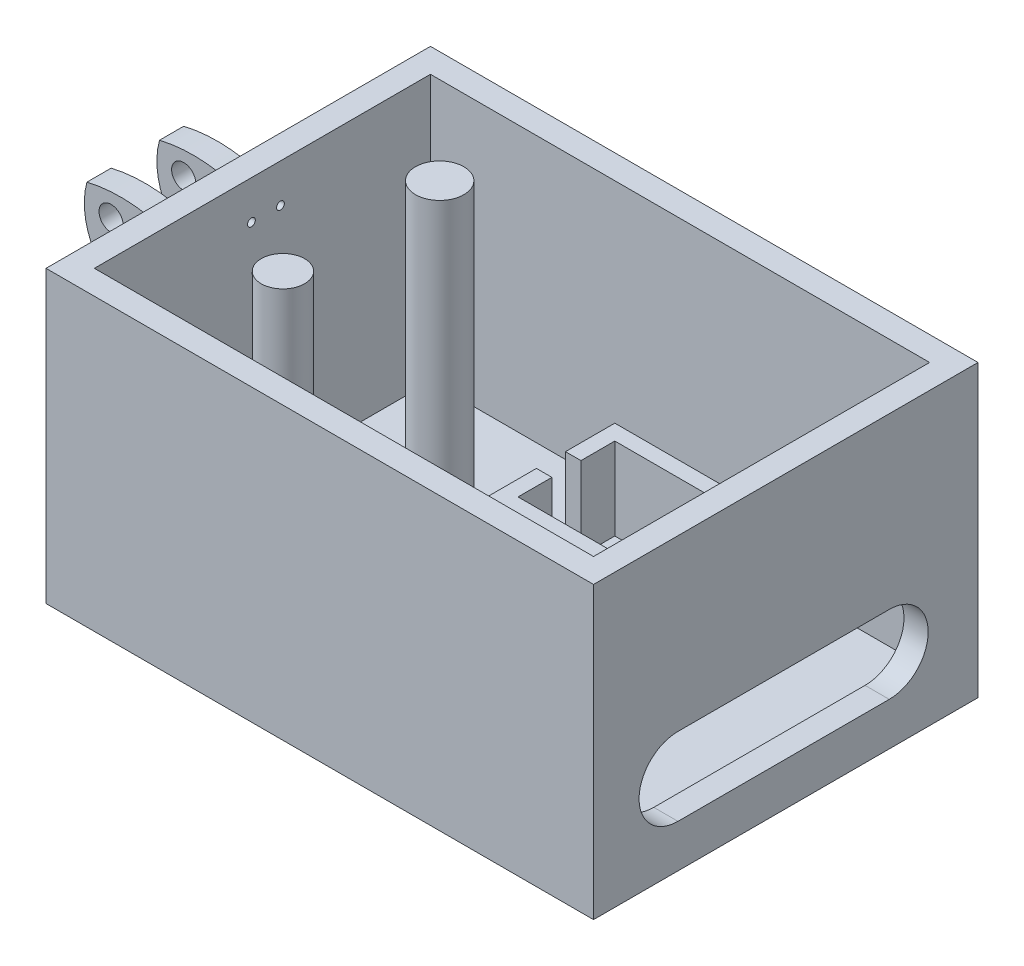
SolidWorks part; units mm, degrees
ref_plane "Front Plane" through (0, 0, 0) normal (0, 0, 1) x (1, 0, 0)
ref_plane "Top Plane" through (0, 0, 0) normal (0, 1, 0) x (1, 0, 0)
ref_plane "Right Plane" through (0, 0, 0) normal (1, 0, 0) x (0, 0, -1)
ref_plane "Palm Side Plane" through (0, 38.1, 0) normal (0, 1, 0) x (1, 0, 0)
ref_plane "Left Side Plane" through (0, 0, 63.5) normal (0, 0, 1) x (1, 0, 0)
ref_plane "Top Side Plane" through (-69.85, 0, 0) normal (1, 0, 0) x (0, 0, -1)
ref_plane "Wrist Plane" through (62.9138, 0, 0) normal (1, 0, 0) x (0, 0, -1)
sketch "Hand Direction Arrow" plane through (0, 38.1, 0) normal (0, 1, 0) x (1, 0, 0)
  line L0 (49.8191, -114.0829) -> (-36.738, -114.0829) construction
  line L1 (-36.738, -114.0829) -> (-22.4792, -131.555) construction
  line L2 (-36.738, -114.0829) -> (-22.4792, -99.8241) construction
sketch "Sketch2" plane through (0, 0, 0) normal (0, 1, 0) x (1, 0, 0)
  line L5 (-69.85, -63.5) -> (69.85, 63.5) construction
  line L6 (-69.85, 63.5) -> (69.85, -63.5) construction
  line L7 (-20.7784, 52.7587) -> (-36.189, 52.7587)
  line L8 (-36.189, 52.7587) -> (-36.189, 33.7087)
  line L16 (-38.8642, 27.3587) -> (-36.189, 33.7087)
  line L19 (15.3118, -63.2103) -> (-3.7382, -63.2103)
  line L20 (-3.7382, -63.2103) -> (-3.7382, -58.593)
  line L21 (22.9098, -62.5249) -> (22.9098, 48.896)
  line L22 (-48.9477, 8.3087) -> (-48.9477, 27.3587)
  line L23 (-48.9477, 27.3587) -> (-38.8642, 27.3587)
  line L24 (-48.9477, 8.3087) -> (-48.9477, -42.4913)
  line L25 (-42.9594, -42.4913) -> (-48.9477, -42.4913)
  arc A0 (22.9098, 48.896) -> (-20.7784, 52.7587) centre (-16.6219, -149.2259) ccw
  arc A2 (-42.9594, -42.4913) -> (-16.4221, -49.7553) centre (-56.8306, -145.2734) cw
  arc A5 (-3.7382, -58.593) -> (-16.4221, -49.7553) centre (16.7508, -15.6666) cw
  arc A6 (15.3118, -63.2103) -> (22.9098, -62.5249) centre (14.5642, -12.4678) ccw
  point P0 (0, 0)
  dimension "D1" = 19.05
  dimension "D4" = 19.05
  dimension "D5" = 19.05
  dimension "D6" = 6.35
extrude "Boss-Extrude1" add sketch "Sketch2" along normal blind 38.1
sketch "Sketch3" plane through (0, 38.1, 0) normal (0, 1, 0) x (1, 0, 0)
  line L5 (-45.7727, 24.1837) -> (19.7348, 24.1837)
  line L6 (22.9098, -62.5249) -> (22.9098, 48.896) construction
  line L24 (-45.7727, 7.713) -> (-45.7727, 24.1837)
  line L26 (-48.9477, 27.3587) -> (-48.9477, -42.4913) construction
  line L41 (-38.8642, 27.3587) -> (22.9098, 27.3587)
  line L42 (-45.7727, 7.713) -> (-45.7727, -19.9216)
  line L44 (-45.7727, -19.9216) -> (19.7348, -19.9216)
  line L45 (19.7348, -19.9216) -> (19.7348, 24.1837)
  line L46 (-48.9477, -23.0966) -> (22.9098, -23.0966)
  line L47 (-48.9477, -55.2233) -> (-48.9477, -23.0966)
  line L48 (-48.9477, 27.3587) -> (-48.9477, -42.4913) construction
  arc A7 (-48.9477, -55.2233) -> (22.9098, -23.0966) centre (8.6461, -87.618) ccw
  arc A11 (-38.8642, 27.3587) -> (22.9098, 27.3587) centre (-7.9772, 76.0331) cw
  point P0 (0, 0)
  point P6 (-45.5127, -25.7954)
  point P29 (-45.5127, -25.7954)
  dimension "D2" = 3.175
  dimension "D3" = 3.175
  dimension "D4" = 3.175
  dimension "D11" = 3.175
extrude "Cut-Extrude1" cut sketch "Sketch3" against normal blind 34.925
sketch "Sketch6" plane through (0, 0, 0) normal (0, 1, 0) x (1, 0, 0)
  line L0 (-18.154, -9.4667) -> (-16.122, -9.4667)
  line L7 (8.008, -13.9117) -> (-16.122, -13.9117)
  line L8 (8.008, -13.9117) -> (8.008, -9.4667)
  line L9 (8.008, -1.2117) -> (-16.122, -1.2117)
  line L10 (-16.122, -13.9117) -> (-16.122, -9.4667)
  line L11 (8.008, -13.9117) -> (-16.122, -1.2117) construction
  line L12 (8.008, -1.2117) -> (-16.122, -13.9117) construction
  line L13 (10.04, -15.9437) -> (-18.154, -15.9437)
  line L14 (10.04, -15.9437) -> (10.04, -9.4667)
  line L15 (10.04, 0.8203) -> (-18.154, 0.8203)
  line L16 (-18.154, -15.9437) -> (-18.154, -9.4667)
  line L17 (10.04, -15.9437) -> (-18.154, 0.8203) construction
  line L18 (10.04, 0.8203) -> (-18.154, -15.9437) construction
  line L19 (-18.154, -5.6567) -> (-16.122, -5.6567)
  line L20 (-18.154, -5.6567) -> (-18.154, 0.8203)
  line L21 (-16.122, -5.6567) -> (-16.122, -1.2117)
  line L22 (8.008, -9.4667) -> (10.04, -9.4667)
  line L23 (8.008, -5.6567) -> (10.04, -5.6567)
  line L24 (8.008, -5.6567) -> (8.008, -1.2117)
  line L25 (10.04, -5.6567) -> (10.04, 0.8203)
  point P0 (26.0547, 16.5381)
  point P6 (-4.057, -7.5617)
  point P29 (-4.057, -7.5617)
  dimension "D6" = 2.032
  dimension "D7" = 2.032
  dimension "D9" = 12.7
  dimension "D10" = 24.13
  dimension "D11" = 4.445
  dimension "D12" = 4.445
  dimension "D13" = 4.445
  dimension "D14" = 4.445
extrude "Servo Box 1" add sketch "Sketch6" along normal blind 13.97
sketch "Sketch7" plane through (0, 0, 0) normal (0, 1, 0) x (1, 0, 0)
  line L0 (-18.154, 10.4723) -> (-16.122, 10.4723)
  line L5 (10.04, 0.8203) -> (-18.154, 0.8203) construction
  line L6 (-18.154, 0.8203) -> (-18.154, -5.6567) construction
  line L7 (8.008, 6.0273) -> (-16.122, 6.0273)
  line L8 (8.008, 6.0273) -> (8.008, 10.4723)
  line L9 (8.008, 18.7273) -> (-16.122, 18.7273)
  line L10 (-16.122, 6.0273) -> (-16.122, 10.4723)
  line L11 (8.008, 6.0273) -> (-16.122, 18.7273) construction
  line L12 (8.008, 18.7273) -> (-16.122, 6.0273) construction
  line L13 (10.04, 3.9953) -> (-18.154, 3.9953)
  line L14 (10.04, 3.9953) -> (10.04, 10.4723)
  line L15 (10.04, 20.7593) -> (-18.154, 20.7593)
  line L16 (-18.154, 3.9953) -> (-18.154, 10.4723)
  line L17 (10.04, 3.9953) -> (-18.154, 20.7593) construction
  line L18 (10.04, 20.7593) -> (-18.154, 3.9953) construction
  line L19 (-18.154, 14.2823) -> (-16.122, 14.2823)
  line L20 (-18.154, 14.2823) -> (-18.154, 20.7593)
  line L21 (-16.122, 14.2823) -> (-16.122, 18.7273)
  line L22 (8.008, 10.4723) -> (10.04, 10.4723)
  line L23 (8.008, 14.2823) -> (10.04, 14.2823)
  line L24 (8.008, 14.2823) -> (8.008, 18.7273)
  line L25 (10.04, 14.2823) -> (10.04, 20.7593)
  point P0 (-14.8998, -5.4903)
  point P6 (-4.057, 12.3773)
  point P29 (-4.057, 12.3773)
  dimension "D2" = 3.175
  dimension "D3" = 0
  dimension "D6" = 2.032
  dimension "D7" = 2.032
  dimension "D9" = 12.7
  dimension "D10" = 24.13
  dimension "D11" = 4.445
  dimension "D12" = 4.445
  dimension "D13" = 4.445
  dimension "D14" = 4.445
extrude "Servo Box 2" add sketch "Sketch7" along normal blind 13.97
ref_plane "Pinky Attachment Plane" through (0, 0, -52.7587) normal (0, 0, -1) x (-1, 0, 0)
ref_plane "Ring Attachment Plane" through (0, 0, -12.1187) normal (0, 0, -1) x (-1, 0, 0)
ref_plane "Middle Attachment Plane" through (0, 0, 13.2813) normal (0, 0, -1) x (-1, 0, 0)
ref_plane "Pointer Attachment Plane" through (0, 0, 38.6813) normal (0, 0, -1) x (-1, 0, 0)
ref_plane "Thumb Attachment Plane" through (-3.7382, 0, 0) normal (-1, 0, 0) x (0, 0, 1)
sketch "Sketch36" plane through (0, 0, -12.1187) normal (0, 0, -1) x (-1, 0, 0)
  line L3 (48.9477, 29.21) -> (48.9477, 18.0742)
  line L5 (48.9477, 18.0742) -> (53.3927, 18.0742)
  line L6 (53.3927, 38.1) -> (53.3927, 18.0742) construction
  line L7 (48.9477, 38.1) -> (48.9477, 0) construction
  line L8 (53.3927, 18.0742) -> (59.7427, 18.0742)
  line L9 (59.7427, 18.0742) -> (59.7427, 21.2492)
  line L10 (-22.9098, 38.1) -> (48.9477, 38.1) construction
  arc A0 (62.9177, 31.242) -> (59.7427, 21.2492) centre (53.6065, 28.6996) cw
  circle A1 centre (59.7427, 28.7074) radius 1.5875
  arc A2 (48.9477, 29.21) -> (62.9177, 31.242) centre (58.4796, 12.7162) cw
  dimension "D1" = 4.445
  dimension "D2" = 10.795
  dimension "D3" = 13.97
  dimension "D5" = 10.795
  dimension "D4" = 6.858
  dimension "D6" = 3.175
extrude "Ring Attachment" add sketch "Sketch36" against normal blind 19.05
sketch "Sketch40" plane through (0, 38.1, 0) normal (0, 1, 0) x (1, 0, 0)
  line L33 (-45.7727, 24.1837) -> (-45.7727, -19.9216) construction
  line L34 (-48.9477, -6.9313) -> (-48.9477, -3.7563)
  line L36 (-48.9477, -3.7563) -> (-65.3617, -3.7563)
  line L37 (-65.3617, -3.7563) -> (-65.3617, -0.5813)
  line L38 (-65.3617, -0.5813) -> (-48.9477, -0.5813)
  line L39 (-48.9477, -0.5813) -> (-48.9477, 5.7687)
  line L40 (-48.9477, 5.7687) -> (-65.7763, 5.7687)
  line L41 (-65.7763, 5.7687) -> (-65.7763, 8.9437)
  line L42 (-65.7763, 8.9437) -> (-48.9477, 8.9437)
  line L43 (-48.9477, 8.9437) -> (-48.9477, 12.1187)
  line L55 (-48.9477, 27.3587) -> (-48.9477, -23.0966) construction
  arc A5 (-48.9477, -6.9313) -> (-48.9477, 12.1187) centre (-63.2034, 2.5937) cw
  dimension "D11" = 3.175
  dimension "D19" = 3.175
  dimension "D20" = 3.175
  dimension "D22" = 3.175
  dimension "D24" = 3.175
extrude "Attachment Trim" cut sketch "Sketch40" against normal blind 25.4
sketch "Sketch33" plane through (-69.85, 0, 0) normal (1, 0, 0) x (0, 0, -1)
  line L1 (27.3587, 38.1) -> (-23.0966, 38.1) construction
  line L4 (8.9437, 18.0742) -> (8.9437, 29.21) construction
  circle A0 centre (0.6887, 33.02) radius 0.508
  circle A1 centre (4.4987, 33.02) radius 0.508
  dimension "D1" = 4.445
  dimension "D2" = 5.08
  dimension "D3" = 5.08
  dimension "D4" = 3.81
extrude "Ring Finger Holes" cut sketch "Sketch33" along normal blind 31.75
sketch "Sketch41" plane through (62.9138, 0, 0) normal (1, 0, 0) x (0, 0, -1)
  line L0 (-12.0167, 10.7439) -> (15.7102, 10.7439) construction
  line L1 (-12.0167, 15.8519) -> (15.7102, 15.8519)
  line L2 (-12.0167, 5.6359) -> (15.7102, 5.6359)
  arc A0 (-12.0167, 15.8519) -> (-12.0167, 5.6359) centre (-12.0167, 10.7439) ccw
  arc A1 (15.7102, 5.6359) -> (15.7102, 15.8519) centre (15.7102, 10.7439) ccw
  point P2 (1.8468, 10.7439)
extrude "Cord Hole" cut sketch "Sketch41" against normal blind 44.45
sketch "Band Reference Line (Fingers)" plane through (0, 0, 0) normal (0, 0, 1) x (1, 0, 0)
  line L0 (-36.189, 8.89) -> (-63.3567, 8.89) construction
  line L1 (-36.189, 3.175) -> (-36.189, 0) construction
  line L2 (-38.8642, 0) -> (-48.9477, 0) construction
  dimension "D1" = 8.89
sketch "Sketch52" plane through (0, 0, -12.1187) normal (0, 0, -1) x (-1, 0, 0)
  line L6 (52.0794, 6.5758) -> (48.9477, 6.7988)
  line L7 (48.9477, 6.7988) -> (48.9477, 3.6818)
  arc A10 (51.562, 4.8624) -> (48.9477, 3.6818) centre (51.9425, 0.535) ccw
  arc A11 (53.2594, 3.4933) -> (51.562, 4.8624) centre (51.2326, 2.7173) ccw
  arc A12 (51.8755, 1.7634) -> (53.2594, 3.4933) centre (51.1377, 3.7721) ccw
  arc A13 (51.2806, 2.6606) -> (51.8755, 1.7634) centre (51.8765, 2.4099) ccw
  arc A14 (50.0744, 2.3556) -> (51.2806, 2.6606) centre (50.6775, 2.5081) cw
  arc A15 (51.7195, 0.6123) -> (50.0744, 2.3556) centre (51.7196, 2.2603) cw
  arc A16 (54.7171, 4.061) -> (52.0794, 6.5758) centre (51.7621, 3.6024) ccw
  arc A17 (51.7195, 0.6123) -> (54.7171, 4.061) centre (51.7621, 3.6024) ccw
extrude "Ring Hook" add sketch "Sketch52" against normal blind 19.05
sketch "Sketch56" plane through (0, 0, 13.2813) normal (0, 0, -1) x (-1, 0, 0)
  line L4 (59.3076, 8.89) -> (56.7676, 8.89)
  line L6 (59.3076, 6.7988) -> (56.7676, 6.7988)
  line L7 (56.7676, 6.7988) -> (56.7676, 3.6818)
  line L8 (56.7676, 12.007) -> (56.7676, 8.89)
  arc A0 (59.3076, 14.3236) -> (62.0244, 11.6068) centre (59.3076, 11.6068) cw
  arc A1 (62.0244, 11.6068) -> (59.3076, 8.89) centre (59.3076, 11.6068) cw
  arc A2 (59.3076, 14.3236) -> (58.1015, 13.0471) centre (59.3428, 13.0823) ccw
  arc A3 (58.1015, 13.0471) -> (58.8022, 13.067) centre (58.4518, 13.057) ccw
  arc A4 (58.8022, 13.067) -> (59.3428, 13.6986) centre (59.4487, 13.0608) cw
  arc A5 (59.3428, 13.6986) -> (61.2287, 11.7836) centre (59.0992, 11.5725) cw
  arc A6 (61.2287, 11.7836) -> (59.3076, 9.9198) centre (59.0785, 12.0779) cw
  arc A7 (59.3076, 9.9198) -> (56.7676, 12.007) centre (60.5905, 14.0702) cw
  arc A10 (59.3076, 5.7689) -> (56.7676, 3.6818) centre (60.5905, 1.6186) ccw
  arc A11 (61.2287, 3.9052) -> (59.3076, 5.7689) centre (59.0785, 3.6108) ccw
  arc A12 (59.3428, 1.9902) -> (61.2287, 3.9052) centre (59.0992, 4.1162) ccw
  arc A13 (58.8022, 2.6218) -> (59.3428, 1.9902) centre (59.4487, 2.628) ccw
  arc A14 (58.1015, 2.6417) -> (58.8022, 2.6218) centre (58.4518, 2.6318) cw
  arc A15 (59.3076, 1.3652) -> (58.1015, 2.6417) centre (59.3428, 2.6065) cw
  arc A16 (62.0244, 4.082) -> (59.3076, 6.7988) centre (59.3076, 4.082) ccw
  arc A17 (59.3076, 1.3652) -> (62.0244, 4.082) centre (59.3076, 4.082) ccw
extrude "Middle Hook" add sketch "Sketch56" against normal blind 19.05 separate body
sketch "Sketch57" plane through (0, 0, 13.2813) normal (0, 0, -1) x (-1, 0, 0)
  line L1 (56.7676, 15.0568) -> (63.2114, 15.0568)
  line L2 (56.7676, 15.0568) -> (56.7676, 7.7531)
  line L3 (56.7676, 7.7531) -> (63.2114, 7.7531)
  line L4 (63.2114, 15.0568) -> (63.2114, 7.7531)
extrude "Middle Hook Cut 1" cut sketch "Sketch57" against normal blind 19.05
sketch "Band Reference Line (Thumb)" plane through (-3.7382, 0, 0) normal (-1, 0, 0) x (0, 0, 1)
  line L0 (58.593, 8.89) -> (76.2209, 8.89) construction
  line L1 (58.593, 3.175) -> (58.593, 0) construction
  line L2 (58.593, 0) -> (63.2103, 0) construction
  dimension "D1" = 8.89
sketch "Sketch65" plane through (0, 0, 0) normal (0, 1, 0) x (1, 0, 0)
  line L30 (-54.7525, 12.1187) -> (-54.7525, -6.9313) construction
  line L31 (-48.9477, 14.7165) -> (-54.7525, 14.7165)
  line L32 (-48.9477, 14.7165) -> (-48.9477, 5.1337)
  line L33 (-48.9477, 5.1337) -> (-54.7525, 5.1337)
  line L34 (-54.7525, 14.7165) -> (-54.7525, 5.1337)
  line L35 (-48.9477, -6.9313) -> (-48.9477, 12.1187) construction
  line L36 (-48.9477, 0.0537) -> (-54.7525, 0.0537)
  line L37 (-48.9477, 0.0537) -> (-48.9477, -6.9313)
  line L38 (-48.9477, -6.9313) -> (-54.7525, -6.9313)
  line L39 (-54.7525, 0.0537) -> (-54.7525, -6.9313)
  line L40 (-54.7525, -6.9313) -> (-51.7195, -6.9313) construction
  line L51 (-64.5731, -9.5782) -> (-54.2045, -9.5782)
  line L52 (-64.5731, -9.5782) -> (-64.5731, -36.4922)
  line L53 (-64.5731, -36.4922) -> (-54.2045, -36.4922)
  line L54 (-54.2045, -9.5782) -> (-54.2045, -36.4922)
  dimension "D7" = 5.08
  dimension "D8" = 6.985
extrude "Cut-Extrude9" cut sketch "Sketch65" along normal blind 15.24
sketch "Sketch66" plane through (0, 38.1, 0) normal (0, 1, 0) x (1, 0, 0)
  line L1 (-48.9477, -23.0966) -> (22.9098, -23.0966)
  line L3 (22.9098, 27.3587) -> (-48.9477, 27.3587)
  arc A0 (-48.9477, -23.0966) -> (22.9098, -23.0966) centre (-13.0189, -114.3663) ccw
  arc A1 (-48.9477, 27.3587) -> (22.9098, 27.3587) centre (-13.0189, 70.2201) cw
extrude "Cut-Extrude10" cut sketch "Sketch66" against normal blind 50.8
sketch "Sketch67" plane through (0, 38.1, 0) normal (0, 1, 0) x (1, 0, 0)
  line L0 (-16.122, -9.4667) -> (-18.154, -9.4667) construction
  line L1 (-18.154, 14.2823) -> (-16.122, 14.2823) construction
  line L2 (-45.7727, 24.1837) -> (-45.7727, -19.9216) construction
  line L3 (-45.7727, 24.1837) -> (-45.7727, -19.9216) construction
  circle A0 centre (-33.0727, -7.8792) radius 2.849
  circle A1 centre (-33.0727, 12.6948) radius 3.175
  dimension "D1" = 1.5875
  dimension "D2" = 1.5875
  dimension "D3" = 12.7
  dimension "D4" = 12.7
extrude "Boss-Extrude2" add sketch "Sketch67" against normal blind 38.1
